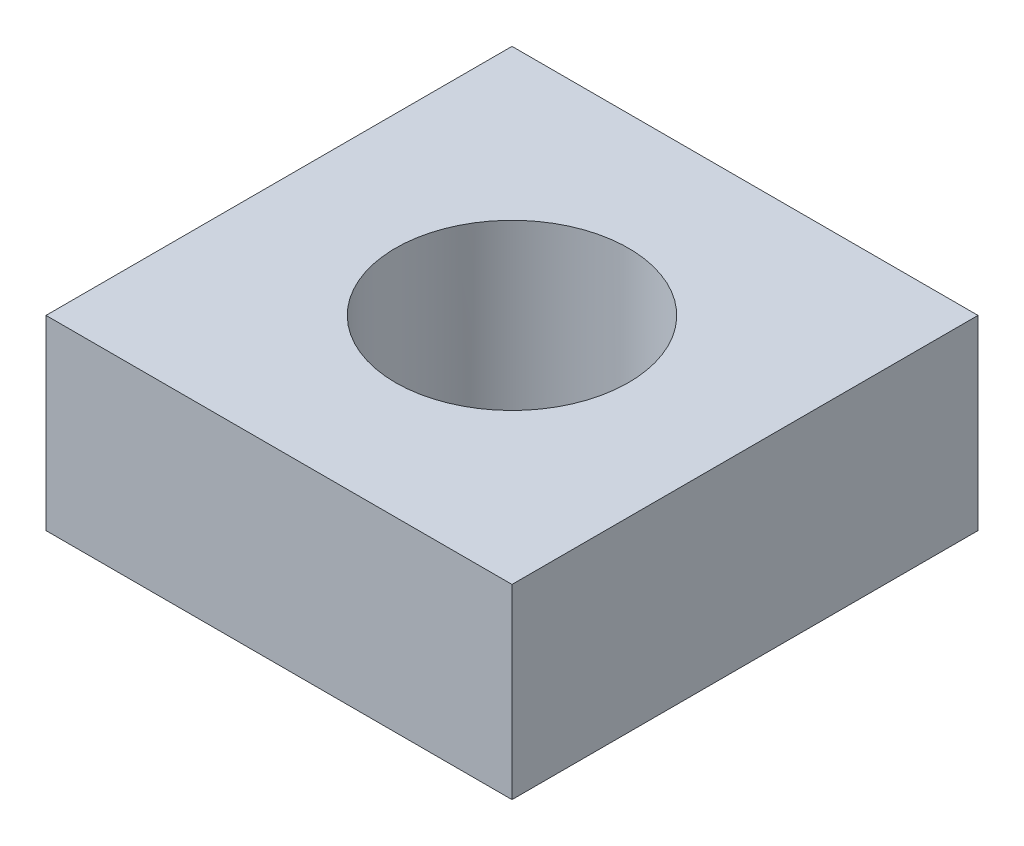
SolidWorks part; units mm, degrees
ref_plane "Plane1" through (0, 0, 0) normal (0, 0, 1) x (1, 0, 0)
ref_plane "Plane2" through (0, 0, 0) normal (0, 1, 0) x (1, 0, 0)
ref_plane "Plane3" through (0, 0, 0) normal (1, 0, 0) x (0, 0, -1)
sketch "Sketch1" plane through (0, 0, 0) normal (0, 1, 0) x (1, 0, 0)
  line L1 (0, 0) -> (50, 0)
  line L2 (0, 0) -> (0, 50)
  line L3 (0, 50) -> (50, 50)
  line L4 (50, 0) -> (50, 50)
  dimension "D1" = 50
  dimension "D2" = 50
extrude "Boss-Extrude1" add sketch "Sketch1" along normal blind 20
sketch "Sketch2" plane through (0, 20, 0) normal (0, 1, 0) x (1, 0, 0)
  line L0 (0, 0) -> (50, 50) construction
  line L1 (50, 0) -> (0, 50) construction
  circle A0 centre (25, 25) radius 12.5
  dimension "D1" = 25
extrude "Cut-Extrude1" cut sketch "Sketch2" against normal blind 30
